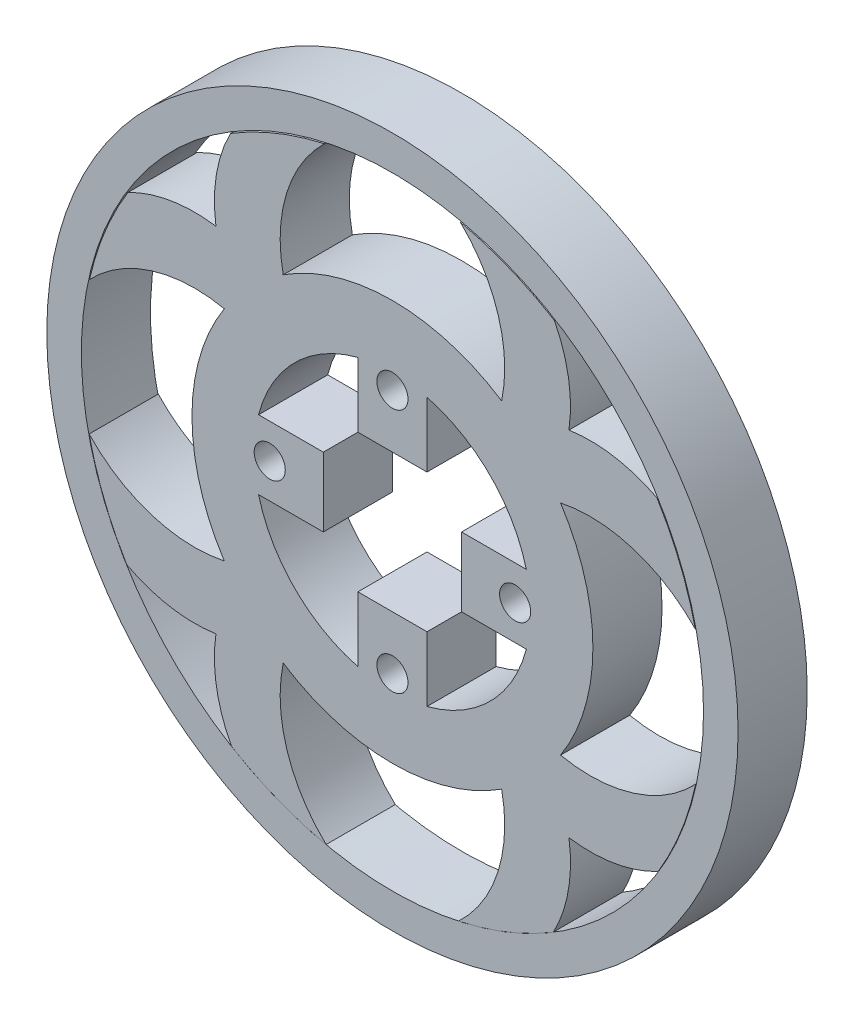
SolidWorks part; units mm, degrees
ref_plane "Front Plane" through (0, 0, 0) normal (0, 0, 1) x (1, 0, 0)
ref_plane "Top Plane" through (0, 0, 0) normal (0, 1, 0) x (1, 0, 0)
ref_plane "Right Plane" through (0, 0, 0) normal (1, 0, 0) x (0, 0, -1)
sketch "Sketch6" plane through (0, 0, 0) normal (0, 0, 1) x (1, 0, 0)
  circle A0 centre (0, 0) radius 20
  circle A1 centre (0, 0) radius 29
  dimension "D1" = 40
  dimension "D2" = 58
extrude "Inner Ring" add sketch "Sketch6" against normal blind 10 separate body
sketch "Sketch7" plane through (0, 0, 0) normal (0, 0, 1) x (1, 0, 0)
  line L2 (-10, 5) -> (-10, -5)
  line L3 (-5, 10) -> (5, 10)
  line L4 (10, 5) -> (10, -5)
  line L5 (-5, -10) -> (5, -10)
  line L14 (-19.3649, 5) -> (-10, 5)
  line L15 (-19.3649, -5) -> (-10, -5)
  line L16 (-5, 19.3649) -> (-5, 10)
  line L17 (5, 19.3649) -> (5, 10)
  line L18 (19.3649, 5) -> (10, 5)
  line L19 (19.3649, -5) -> (10, -5)
  line L20 (5, -19.3649) -> (5, -10)
  line L21 (-5, -19.3649) -> (-5, -10)
  circle A1 centre (0, 0) radius 20
  circle M19 centre (0, 0) radius 20
  dimension "D1" = 20
  dimension "D2" = 20
  dimension "D3" = 10
  dimension "D5" = 10
  dimension "D7" = 10
  dimension "D8" = 10
extrude "Motor Connector Cut" add sketch "Sketch7" against normal blind 10 contours L19 L18 L4 M19 | L17 L16 L3 M19 | L15 L2 L14 M19 | L21 L20 L5 M19
sketch "Sketch8" plane through (0, 0, 0) normal (0, 0, 1) x (1, 0, 0)
  circle A1 centre (0, 17.75) radius 2.25
  circle A2 centre (17.75, 0) radius 2.25
  circle A3 centre (0, -17.75) radius 2.25
  circle A4 centre (-17.75, 0) radius 2.25
  dimension "D1" = 4.5
  dimension "D2" = 4.5
  dimension "D3" = 4.5
  dimension "D4" = 4.5
sketch "Sketch9" plane through (0, 0, 0) normal (0, 0, 1) x (1, 0, 0)
  circle A0 centre (0, 0) radius 50
  circle A18 centre (0, 0) radius 29
  dimension "D2" = 100
extrude "Outside Ring Extrusion" add sketch "Sketch9" against normal blind 10
sketch "Sketch12" plane through (0, 0, 0) normal (0, 0, 1) x (1, 0, 0)
  circle A0 centre (0, 0) radius 27.5
  circle A1 centre (0, 0) radius 45
  dimension "D1" = 55
  dimension "D2" = 90
extrude "Cut-Extrude6" cut sketch "Sketch12" against normal blind 55
extrude "Motor Connector Holes" cut sketch "Sketch8" against normal blind 10
sketch "Sketch10" plane through (0, 0, 0) normal (0, 0, 1) x (1, 0, 0)
  circle A0 centre (0, 0) radius 29
  arc A4 (-24.0947, 20.4191) -> (-41.6064, 16.7952) centre (-29, 0) ccw
  circle A5 centre (0, 0) radius 50
  arc A6 (-0.0957, 0) -> (0, 0.0957) centre (-17.7016, 17.7016) ccw
  arc A9 (-28.6072, 4.7568) -> (-42.4805, -14.6492) centre (-17.7016, -17.7016) ccw
  arc A10 (-20.4191, 24.0947) -> (-38.2638, 23.4049) centre (-28.6072, 4.7568) ccw
  arc A11 (-24.3176, 15.8004) -> (-43.8179, 9.722) centre (-28.6072, -4.7568) ccw
  circle A18 centre (0, 0) radius 29
  arc A19 (14.3758, 42.4453) -> (-4.7568, 28.6072) centre (17.7016, 17.7016) ccw
  circle A20 centre (0, -0.0957) radius 44.9043
  arc A21 (24.3176, -15.8004) -> (43.8731, -9.6638) centre (28.6072, 4.7568) ccw
  arc A22 (43.8179, 9.722) -> (24.3176, 15.8004) centre (28.6072, -4.7568) ccw
  arc A23 (41.6064, 16.7952) -> (21.3966, 19.5752) centre (29, 0) ccw
  arc A24 (49.5968, 4.0954) -> (49.3228, 8.2014) centre (28.6072, 4.7568) ccw
  arc A25 (49.5968, -4.0954) -> (49.5968, 4.0954) centre (29, 0) ccw
  arc A26 (28.6072, -4.7568) -> (42.4628, 14.5092) centre (17.7016, 17.7016) ccw
  arc A27 (42.4805, -14.6492) -> (28.6072, 4.7568) centre (17.7016, -17.7016) ccw
  arc A28 (49.3228, -8.2014) -> (49.5968, -4.0954) centre (28.6072, -4.7568) ccw
  arc A29 (25.5301, 25.5301) -> (23.4328, 38.2096) centre (4.7568, 28.6072) ccw
  arc A30 (23.2856, -38.4907) -> (22.8197, -17.8959) centre (4.7568, -28.6072) ccw
  arc A31 (20.4191, 24.0947) -> (16.8561, 41.5248) centre (0, 29) ccw
  arc A32 (24.0947, -20.4191) -> (41.717, -16.7116) centre (29, 0) ccw
  arc A33 (15.8004, 24.3176) -> (9.8231, 43.721) centre (-4.7568, 28.6072) ccw
  arc A34 (4.7568, 28.6072) -> (-14.3758, 42.4453) centre (-17.7016, 17.7016) ccw
  arc A35 (16.6483, -41.7998) -> (20.4191, -24.0947) centre (0, -29) ccw
  arc A36 (9.5599, -43.9706) -> (15.8004, -24.3176) centre (-4.7568, -28.6072) ccw
  arc A38 (17.8959, -22.8197) -> (38.435, -23.3152) centre (28.6072, -4.7568) ccw
  arc A39 (-14.7836, -42.4967) -> (4.7568, -28.6072) centre (-17.7016, -17.7016) ccw
  arc A40 (-38.435, -23.3152) -> (-20.4191, -24.0947) centre (-28.6072, -4.7568) ccw
  arc A41 (-43.8731, -9.6638) -> (-24.3176, -15.8004) centre (-28.6072, 4.7568) ccw
  arc A43 (-41.717, -16.7116) -> (-21.3966, -19.5752) centre (-29, 0) ccw
  arc A44 (0, -0.0957) -> (-0.0957, 0) centre (-17.7016, -17.7016) ccw
  arc A45 (-42.4628, 14.5092) -> (-28.6072, -4.7568) centre (-17.7016, 17.7016) ccw
  arc A46 (-4.7568, -28.6072) -> (14.7836, -42.4967) centre (17.7016, -17.7016) ccw
  arc A47 (-23.4328, 38.2096) -> (-24.0947, 20.4191) centre (-4.7568, 28.6072) ccw
  arc A48 (-15.8004, -24.3176) -> (-9.5599, -43.9706) centre (4.7568, -28.6072) ccw
  arc A49 (-16.8561, 41.5248) -> (-19.5752, 21.3966) centre (0, 29) ccw
  arc A50 (-20.4191, -24.0947) -> (-16.6483, -41.7998) centre (0, -29) ccw
  arc A51 (-9.8231, 43.721) -> (-15.8004, 24.3176) centre (4.7568, 28.6072) ccw
  arc A52 (-25.5301, -25.5301) -> (-23.2856, -38.4907) centre (-4.7568, -28.6072) ccw
  arc A53 (4.0954, 49.5968) -> (-4.0954, 49.5968) centre (0, 29) ccw
  arc A54 (8.2014, 49.3228) -> (0, 49.0614) centre (4.7568, 28.6072) ccw
  arc A55 (0, 49.0614) -> (-8.2014, 49.3228) centre (-4.7568, 28.6072) ccw
  arc A56 (38.2638, 23.4049) -> (25.5301, 25.5301) centre (28.6072, 4.7568) ccw
  circle A57 centre (-0.0957, 0) radius 27.4043
extrude "Boss-Extrude4" add sketch "Sketch10" against normal blind 10
